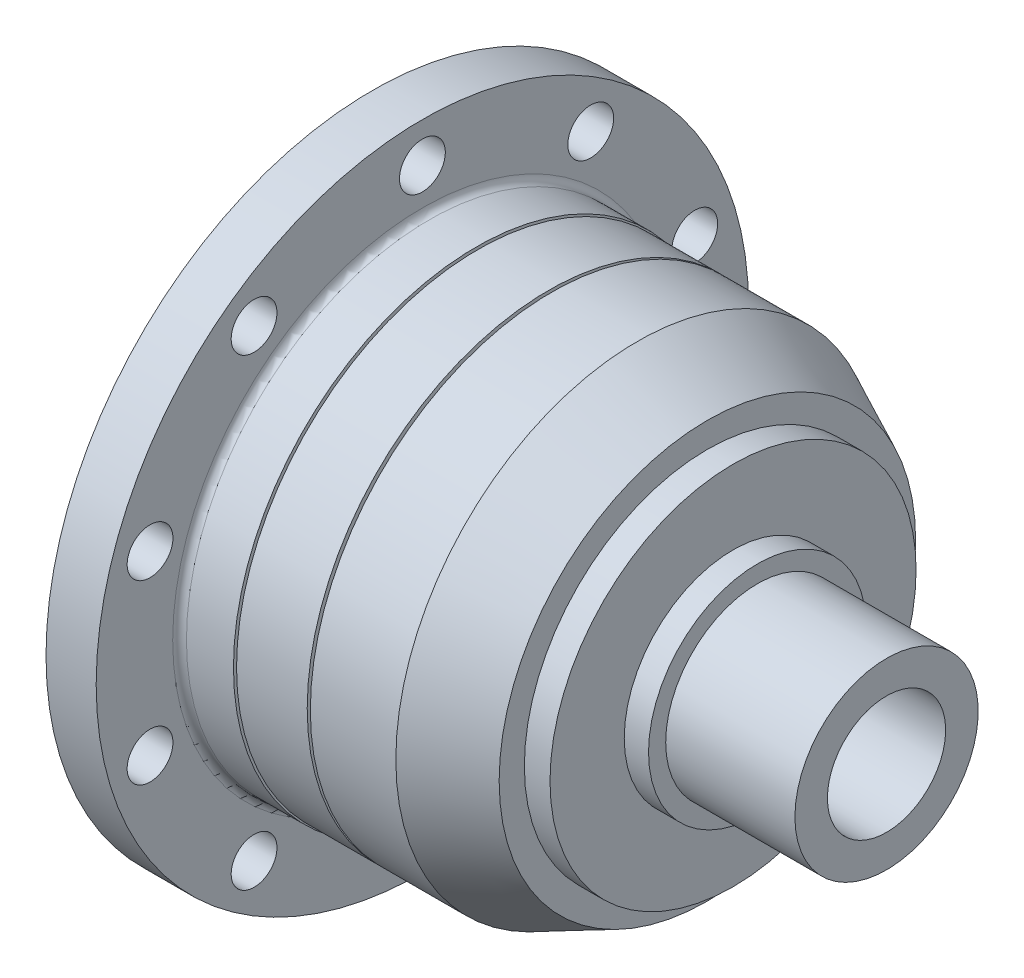
SolidWorks part; units mm, degrees
material "Plain Carbon Steel"
ref_plane "Front Plane" through (0, 0, 0) normal (0, 0, 1) x (1, 0, 0)
ref_plane "Top Plane" through (0, 0, 0) normal (0, 1, 0) x (1, 0, 0)
ref_plane "Right Plane" through (0, 0, 0) normal (1, 0, 0) x (0, 0, -1)
sketch "Sketch1" plane through (0, 0, 0) normal (0, 0, 1) x (1, 0, 0)
  line L0 (-78.8432, 0) -> (101.6, 0) construction
  line L1 (0, 53) -> (0, 71.2)
  line L2 (0, 71.2) -> (-10.95, 71.2)
  line L3 (-10.95, 71.2) -> (-10.95, 42.0874)
  line L5 (-10.95, 42.0874) -> (-10.95, 24.85)
  line L6 (-10.95, 24.85) -> (-12.95, 24.85)
  line L7 (-12.95, 24.85) -> (-12.95, 20)
  line L8 (-12.95, 20) -> (-34.5, 20)
  line L9 (-34.5, 20) -> (-34.5, 12.9)
  line L10 (-34.5, 12.9) -> (101.3, 12.9)
  line L11 (0, 53) -> (11.761, 53)
  line L12 (11.761, 50.1226) -> (12.1319, 50.1226)
  line L13 (12.1319, 50.1226) -> (12.1319, 52.7)
  line L14 (12.1319, 52.7) -> (27.5591, 52.7)
  line L15 (27.5591, 52.7) -> (27.5591, 51.3493)
  line L16 (27.5591, 51.3493) -> (28.2404, 51.3493)
  line L17 (28.2404, 51.3493) -> (28.2404, 52.7)
  line L18 (28.2404, 52.7) -> (46.9, 52.7)
  line L19 (11.761, 53) -> (11.761, 50.1226)
  line L21 (46.9, 52.7) -> (62.2, 45.45)
  line L22 (62.2, 45.45) -> (62.2, 39.95)
  line L23 (62.2, 39.95) -> (67.8, 39.95)
  line L24 (67.8, 39.95) -> (67.8, 23.75)
  line L25 (67.8, 23.75) -> (73.1, 23.75)
  line L26 (73.1, 23.75) -> (73.1, 20)
  line L27 (73.1, 20) -> (101.3, 20)
  line L28 (101.3, 20) -> (101.3, 12.9)
  line L29 (-9.3976, 62.5) -> (4.5792, 62.5) construction
  dimension "D1" = 40
  dimension "D2" = 25.8
  dimension "D3" = 135.8
  dimension "D4" = 105.4
  dimension "D5" = 62.2
  dimension "D6" = 28.2
  dimension "D7" = 2
  dimension "D8" = 62.5
  dimension "D9" = 47.5
  dimension "D10" = 79.9
  dimension "D11" = 5.3
  dimension "D12" = 5.6
  dimension "D13" = 15.3
  dimension "D14" = 90.9
  dimension "D15" = 0.3
  dimension "D16" = 142.4
  dimension "D17" = 10.95
  dimension "D18" = 49.7
revolve "Revolve1" add sketch "Sketch1"
sketch "Sketch2" plane through (-10.95, 0, 0) normal (-1, 0, 0) x (0, 0, 1)
  circle A0 centre (0, 62.5) radius 5
  circle A1 centre (36.7366, 50.5636) radius 5
  circle A2 centre (59.441, 19.3136) radius 5
  circle A3 centre (59.441, -19.3136) radius 5
  circle A4 centre (36.7366, -50.5636) radius 5
  circle A5 centre (0, -62.5) radius 5
  circle A6 centre (-36.7366, -50.5636) radius 5
  circle A7 centre (-59.441, -19.3136) radius 5
  circle A8 centre (-59.441, 19.3136) radius 5
  circle A9 centre (-36.7366, 50.5636) radius 5
  dimension "D2" = 10
  dimension "D1" = 62.5
extrude "Extrude1" cut sketch "Sketch2" against normal up to surface (10.95 mm away) up to face at (0, 0, 71.2)
sketch "Sketch3" plane through (0, 0, 0) normal (0, 0, 1) x (1, 0, 0)
  line L0 (33.4, 69.5718) -> (33.4, -69.5718) construction
  line L1 (33.4, 0) -> (-34.5, 0) construction
  line L2 (-34.5, 20) -> (-34.5, -20) construction
  line L3 (33.4, 0) -> (101.3, 0) construction
  line L4 (101.3, -20) -> (101.3, 20) construction
fillet "Fillet3" radius 1.5 2 edges at (-10.95, 0, 24.85) (0, 0, 53)
sketch "Sketch8" [suppressed] plane through (0, 0, 0) normal (1, 0, 0) x (0, 0, -1)
  line L0 (7, 70.8551) -> (13.3573, 51.2892)
  line L1 (0, 0) -> (0, 77.7288) construction
  line L2 (65.2306, 28.5378) -> (44.6181, 28.6046)
  line L3 (0, 0) -> (93.3042, 30.3164) construction
  circle A0 centre (0, 0) radius 71.2 construction
  circle A1 centre (0, 0) radius 53 construction
  circle A3 centre (0, 0) radius 71.2 construction
  circle A4 centre (0, 0) radius 53 construction
  arc A5 (13.3573, 51.2892) -> (44.6181, 28.6046) centre (0, 0) cw
  arc A6 (7, 70.8551) -> (65.2306, 28.5378) centre (0, 0) cw
  dimension "D1" = 7
  dimension "D2" = 18
  dimension "D4" = 72
extrude "Extrude5" [suppressed] cut sketch "Sketch8" against normal through all
pattern_circular "CirPattern1" [suppressed] count 5 over 360
fillet "Fillet1" [suppressed] radius 10
fillet "Fillet2" [suppressed] radius 10
